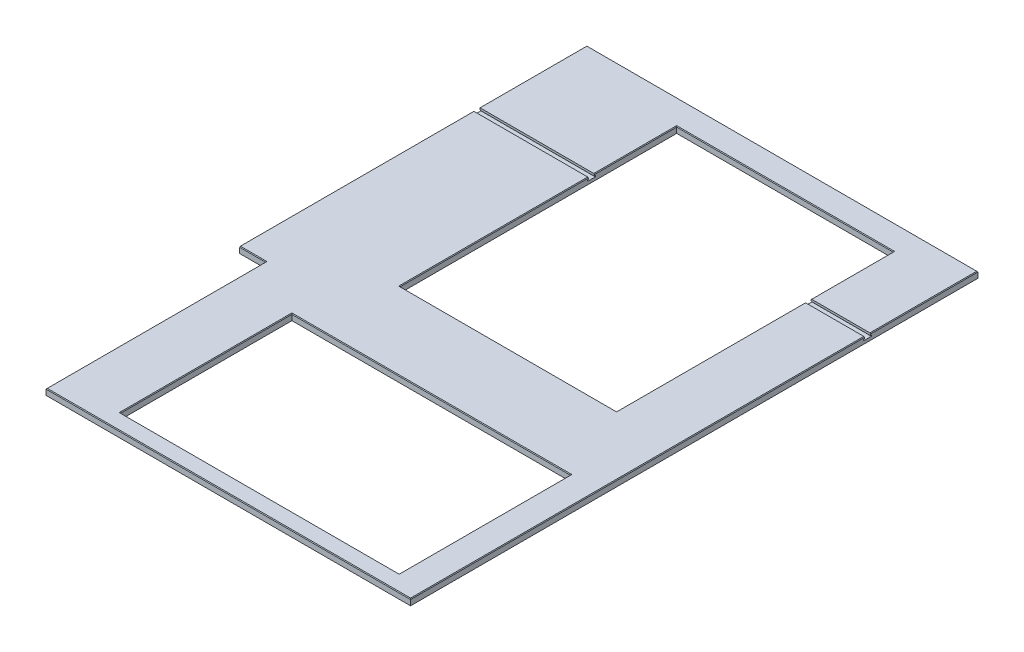
SolidWorks part; units mm, degrees
material "Oak"
ref_plane "Front Plane" through (0, 0, 0) normal (0, 0, 1) x (1, 0, 0)
ref_plane "Top Plane" through (0, 0, 0) normal (0, 1, 0) x (1, 0, 0)
ref_plane "Right Plane" through (0, 0, 0) normal (1, 0, 0) x (0, 0, -1)
sketch "Sketch1" plane through (0, 0, 0) normal (0, 1, 0) x (1, 0, 0)
  line L4 (1219.2, 0) -> (1219.2, 1771.65)
  line L5 (1219.2, 1771.65) -> (0, 1771.65)
  line L7 (0, 0) -> (1219.2, 0)
  line L8 (0, 1771.65) -> (0, 0)
  dimension "D1" = 1219.2
  dimension "D5" = 1771.65
extrude "Boss-Extrude1" add sketch "Sketch1" against normal blind 19.05
sketch "Sketch2" plane through (0, 0, 0) normal (0, 1, 0) x (1, 0, 0)
  line L1 (262.89, 585.7875) -> (1132.84, 585.7875)
  line L2 (262.89, 585.7875) -> (262.89, 50.8)
  line L3 (262.89, 50.8) -> (1132.84, 50.8)
  line L4 (1132.84, 585.7875) -> (1132.84, 50.8)
  dimension "D1" = 869.95
  dimension "D2" = 534.9875
  dimension "D3" = 262.89
  dimension "D4" = 50.8
extrude "Cut-Extrude1" cut sketch "Sketch2" against normal through all
sketch "Sketch3" plane through (0, 0, 0) normal (0, 1, 0) x (1, 0, 0)
  line L0 (0, 0) -> (1219.2, 0) construction
  line L1 (0, 685.8) -> (80.9625, 685.8)
  line L2 (0, 685.8) -> (0, 0)
  line L3 (0, 0) -> (80.9625, 0)
  line L4 (80.9625, 685.8) -> (80.9625, 0)
  line L5 (0, 1771.65) -> (0, 0) construction
  dimension "D1" = 80.9625
  dimension "D3" = 685.8
extrude "Cut-Extrude2" cut sketch "Sketch3" against normal through all
sketch "Sketch4" plane through (0, 0, 0) normal (0, 1, 0) x (1, 0, 0)
  line L1 (357.1875, 1692.91) -> (1033.3888, 1692.91)
  line L2 (357.1875, 1692.91) -> (357.1875, 829.0585)
  line L3 (357.1875, 829.0585) -> (1033.3888, 829.0585)
  line L4 (1033.3888, 1692.91) -> (1033.3888, 829.0585)
  dimension "D1" = 357.1875
  dimension "D2" = 676.2013
  dimension "D3" = 1692.91
  dimension "D4" = 863.8515
extrude "Cut-Extrude3" cut sketch "Sketch4" against normal through all
sketch "Sketch5" plane through (0, 0, 0) normal (-1, 0, 0) x (0, 0, 1)
  line L7 (-1436.1414, 0) -> (-1417.0914, 0)
  line L15 (-1436.1414, 0) -> (-1436.1414, -5.969)
  line L16 (-1436.1414, -5.969) -> (-1438.8084, -5.969)
  line L17 (-1438.8084, -5.969) -> (-1438.8084, -9.525)
  line L18 (-1438.8084, -9.525) -> (-1414.4244, -9.525)
  line L19 (-1414.4244, -9.525) -> (-1414.4244, -5.969)
  line L20 (-1414.4244, -5.969) -> (-1417.0914, -5.969)
  line L21 (-1417.0914, -5.969) -> (-1417.0914, 0)
  line L22 (-1771.65, 0) -> (-685.8, 0) construction
  line L23 (-1426.6164, 0) -> (-1426.6164, -9.525) construction
  line L24 (-1771.65, -19.05) -> (-1771.65, 0) construction
  point P8 (-1415.7579, -5.969)
  dimension "D1" = 9.525
  dimension "D2" = 19.05
  dimension "D3" = 24.384
  dimension "D4" = 5.969
  dimension "D5" = 345.0336
extrude "Cut-Extrude4" cut sketch "Sketch5" against normal through all
chamfer "Chamfer1" distance 2.032 angle 45 16 edges at (357.1875, 0, -1564.5257) (695.2882, 0, -1692.91) (1033.3888, 0, -1564.5257) (1033.3888, 0, -1123.075) (695.2882, 0, -829.0585) (357.1875, 0, -1123.075) (609.6, 0, -1771.65) (1219.2, 0, -1603.8957) (650.0813, 0, 0) (1219.2, 0, -708.5457) (697.865, 0, -50.8) (1132.84, 0, -318.2937) (697.865, 0, -585.7875) (262.89, 0, -318.2937) (40.4813, 0, -685.8) (80.9625, 0, -342.9)
